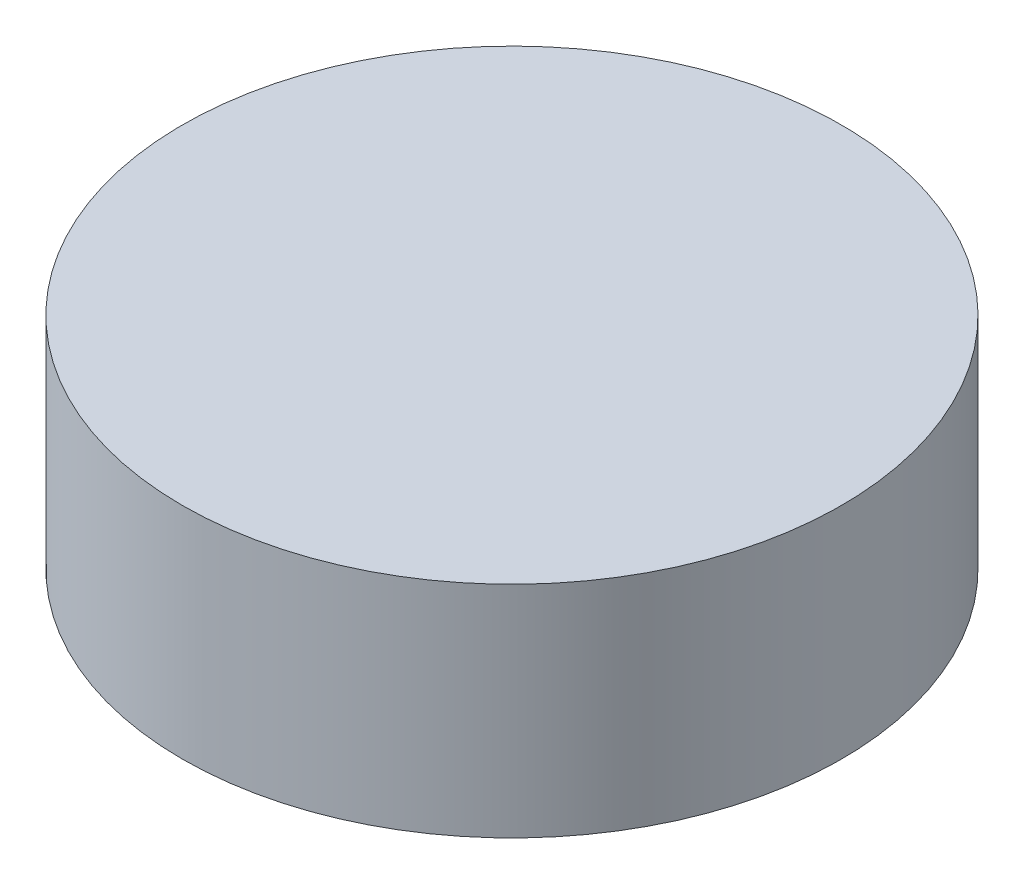
SolidWorks part; units mm, degrees
ref_plane "Front Plane" through (0, 0, 0) normal (0, 0, 1) x (1, 0, 0)
ref_plane "Top Plane" through (0, 0, 0) normal (0, 1, 0) x (1, 0, 0)
ref_plane "Right Plane" through (0, 0, 0) normal (1, 0, 0) x (0, 0, -1)
sketch "Sketch1" plane through (0, 0, 0) normal (0, 1, 0) x (1, 0, 0)
  circle A0 centre (0, 0) radius 3
  dimension "D1" = 6
extrude "Boss-Extrude1" add sketch "Sketch1" along normal blind 2
